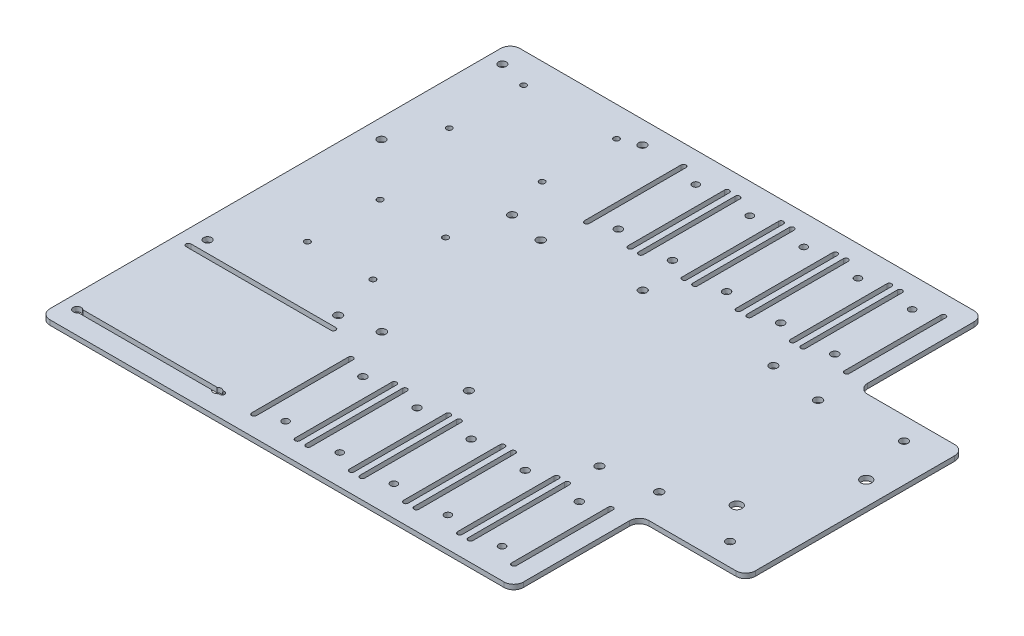
SolidWorks part; units mm, degrees
ref_plane "Front Plane" through (0, 0, 0) normal (0, 0, 1) x (1, 0, 0)
ref_plane "Top Plane" through (0, 0, 0) normal (0, 1, 0) x (1, 0, 0)
ref_plane "Right Plane" through (0, 0, 0) normal (1, 0, 0) x (0, 0, -1)
sketch "Sketch1" plane through (0, 0, 0) normal (0, 1, 0) x (1, 0, 0)
  line L1 (-261.1069, -365.6615) -> (261.1069, -365.6615)
  line L2 (-261.1069, -365.6615) -> (-261.1069, 365.6615)
  line L3 (-261.1069, 365.6615) -> (261.1069, 365.6615)
  line L4 (261.1069, -365.6615) -> (261.1069, 365.6615)
  line L5 (-261.1069, -365.6615) -> (261.1069, 365.6615) construction
  line L6 (-261.1069, 365.6615) -> (261.1069, -365.6615) construction
  point P0 (0, 0)
extrude "Boss-Extrude1" add sketch "Sketch1" along normal blind 3.175
sketch "Sketch3" plane through (0, 3.175, 0) normal (0, 1, 0) x (1, 0, 0)
  line L0 (-86.2012, -141.097) -> (-86.2012, -77.597) construction
  line L1 (91.1352, 52.197) -> (-91.1352, 52.197)
  line L2 (91.1352, 52.197) -> (91.1352, -52.197)
  line L3 (91.1352, -52.197) -> (-91.1352, -52.197)
  line L4 (-91.1352, 52.197) -> (-91.1352, -52.197)
  line L5 (91.1352, 52.197) -> (-91.1352, -52.197) construction
  line L6 (91.1352, -52.197) -> (-91.1352, 52.197) construction
  line L7 (-86.2012, -141.097) -> (-57.6262, -141.097)
  line L8 (-86.2012, -141.097) -> (-86.2012, -77.597)
  line L9 (-86.2012, -77.597) -> (-57.6262, -77.597)
  line L10 (-57.6262, -141.097) -> (-57.6262, -77.597)
  line L11 (-87.7887, -141.097) -> (-87.7887, -77.597)
  line L12 (-84.6138, -141.097) -> (-84.6138, -77.597)
  line L13 (-57.6262, -141.097) -> (-57.6262, -77.597) construction
  line L14 (-59.2137, -141.097) -> (-59.2137, -77.597)
  line L15 (-56.0388, -141.097) -> (-56.0388, -77.597)
  line L16 (-50.6412, -141.097) -> (-50.6412, -77.597) construction
  line L17 (-52.2287, -141.097) -> (-52.2287, -77.597)
  line L18 (-49.0538, -141.097) -> (-49.0538, -77.597)
  line L19 (-22.0662, -141.097) -> (-22.0662, -77.597) construction
  line L20 (-23.6537, -141.097) -> (-23.6537, -77.597)
  line L21 (-20.4788, -141.097) -> (-20.4788, -77.597)
  line L22 (-15.0812, -141.097) -> (-15.0812, -77.597) construction
  line L23 (-16.6687, -141.097) -> (-16.6687, -77.597)
  line L24 (-13.4938, -141.097) -> (-13.4938, -77.597)
  line L25 (13.4938, -141.097) -> (13.4938, -77.597) construction
  line L26 (11.9063, -141.097) -> (11.9063, -77.597)
  line L27 (15.0812, -141.097) -> (15.0812, -77.597)
  line L28 (20.4788, -141.097) -> (20.4788, -77.597) construction
  line L29 (18.8913, -141.097) -> (18.8913, -77.597)
  line L30 (22.0662, -141.097) -> (22.0662, -77.597)
  line L31 (49.0538, -141.097) -> (49.0538, -77.597) construction
  line L32 (47.4663, -141.097) -> (47.4663, -77.597)
  line L33 (50.6412, -141.097) -> (50.6412, -77.597)
  line L34 (56.0388, -141.097) -> (56.0388, -77.597) construction
  line L35 (54.4513, -141.097) -> (54.4513, -77.597)
  line L36 (57.6262, -141.097) -> (57.6262, -77.597)
  line L37 (84.6138, -141.097) -> (84.6138, -77.597) construction
  line L38 (83.0263, -141.097) -> (83.0263, -77.597)
  line L39 (86.2012, -141.097) -> (86.2012, -77.597)
  line L40 (-261.1069, 0) -> (261.1069, 0)
  line L41 (-261.1069, 365.6615) -> (-261.1069, -365.6615) construction
  line L42 (261.1069, -365.6615) -> (261.1069, 365.6615) construction
  line L43 (-86.2012, 141.097) -> (-86.2012, 77.597) construction
  line L44 (-87.7887, 141.097) -> (-87.7887, 77.597)
  line L45 (-84.6138, 141.097) -> (-84.6138, 77.597)
  line L46 (-57.6262, 141.097) -> (-57.6262, 77.597) construction
  line L47 (-59.2137, 141.097) -> (-59.2137, 77.597)
  line L48 (-56.0388, 141.097) -> (-56.0388, 77.597)
  line L49 (-50.6412, 141.097) -> (-50.6412, 77.597) construction
  line L50 (-52.2287, 141.097) -> (-52.2287, 77.597)
  line L51 (-49.0538, 141.097) -> (-49.0538, 77.597)
  line L52 (-22.0662, 141.097) -> (-22.0662, 77.597) construction
  line L53 (-23.6537, 141.097) -> (-23.6537, 77.597)
  line L54 (-20.4788, 141.097) -> (-20.4788, 77.597)
  line L55 (-15.0812, 141.097) -> (-15.0812, 77.597) construction
  line L56 (-16.6687, 141.097) -> (-16.6687, 77.597)
  line L57 (-13.4938, 141.097) -> (-13.4938, 77.597)
  line L58 (13.4938, 141.097) -> (13.4938, 77.597) construction
  line L59 (11.9063, 141.097) -> (11.9063, 77.597)
  line L60 (15.0812, 141.097) -> (15.0812, 77.597)
  line L61 (20.4788, 141.097) -> (20.4788, 77.597) construction
  line L62 (18.8913, 141.097) -> (18.8913, 77.597)
  line L63 (22.0662, 141.097) -> (22.0662, 77.597)
  line L64 (49.0538, 141.097) -> (49.0538, 77.597) construction
  line L65 (47.4663, 141.097) -> (47.4663, 77.597)
  line L66 (50.6412, 141.097) -> (50.6412, 77.597)
  line L67 (56.0388, 141.097) -> (56.0388, 77.597) construction
  line L68 (54.4513, 141.097) -> (54.4513, 77.597)
  line L69 (57.6262, 141.097) -> (57.6262, 77.597)
  line L70 (84.6138, 141.097) -> (84.6138, 77.597) construction
  line L71 (83.0263, 141.097) -> (83.0263, 77.597)
  line L72 (86.2012, 141.097) -> (86.2012, 77.597)
  arc A0 (-87.7887, -141.097) -> (-84.6138, -141.097) centre (-86.2012, -141.097) ccw
  arc A1 (-84.6138, -77.597) -> (-87.7887, -77.597) centre (-86.2012, -77.597) ccw
  arc A2 (-59.2137, -141.097) -> (-56.0388, -141.097) centre (-57.6262, -141.097) ccw
  arc A3 (-56.0388, -77.597) -> (-59.2137, -77.597) centre (-57.6262, -77.597) ccw
  arc A4 (-52.2287, -141.097) -> (-49.0538, -141.097) centre (-50.6412, -141.097) ccw
  arc A5 (-49.0538, -77.597) -> (-52.2287, -77.597) centre (-50.6412, -77.597) ccw
  arc A6 (-23.6537, -141.097) -> (-20.4788, -141.097) centre (-22.0662, -141.097) ccw
  arc A7 (-20.4788, -77.597) -> (-23.6537, -77.597) centre (-22.0662, -77.597) ccw
  arc A8 (-16.6687, -141.097) -> (-13.4938, -141.097) centre (-15.0812, -141.097) ccw
  arc A9 (-13.4938, -77.597) -> (-16.6687, -77.597) centre (-15.0812, -77.597) ccw
  arc A10 (11.9063, -141.097) -> (15.0812, -141.097) centre (13.4938, -141.097) ccw
  arc A11 (15.0812, -77.597) -> (11.9063, -77.597) centre (13.4938, -77.597) ccw
  arc A12 (18.8913, -141.097) -> (22.0662, -141.097) centre (20.4788, -141.097) ccw
  arc A13 (22.0662, -77.597) -> (18.8913, -77.597) centre (20.4788, -77.597) ccw
  arc A14 (47.4663, -141.097) -> (50.6412, -141.097) centre (49.0538, -141.097) ccw
  arc A15 (50.6412, -77.597) -> (47.4663, -77.597) centre (49.0538, -77.597) ccw
  arc A16 (54.4513, -141.097) -> (57.6262, -141.097) centre (56.0388, -141.097) ccw
  arc A17 (57.6262, -77.597) -> (54.4513, -77.597) centre (56.0388, -77.597) ccw
  arc A18 (83.0263, -141.097) -> (86.2012, -141.097) centre (84.6138, -141.097) ccw
  arc A19 (86.2012, -77.597) -> (83.0263, -77.597) centre (84.6138, -77.597) ccw
  arc A20 (-87.7887, 141.097) -> (-84.6138, 141.097) centre (-86.2012, 141.097) cw
  arc A21 (-84.6138, 77.597) -> (-87.7887, 77.597) centre (-86.2012, 77.597) cw
  arc A22 (-59.2137, 141.097) -> (-56.0388, 141.097) centre (-57.6262, 141.097) cw
  arc A23 (-56.0388, 77.597) -> (-59.2137, 77.597) centre (-57.6262, 77.597) cw
  arc A24 (-52.2287, 141.097) -> (-49.0538, 141.097) centre (-50.6412, 141.097) cw
  arc A25 (-49.0538, 77.597) -> (-52.2287, 77.597) centre (-50.6412, 77.597) cw
  arc A26 (-23.6537, 141.097) -> (-20.4788, 141.097) centre (-22.0662, 141.097) cw
  arc A27 (-20.4788, 77.597) -> (-23.6537, 77.597) centre (-22.0662, 77.597) cw
  arc A28 (-16.6687, 141.097) -> (-13.4938, 141.097) centre (-15.0812, 141.097) cw
  arc A29 (-13.4938, 77.597) -> (-16.6687, 77.597) centre (-15.0812, 77.597) cw
  arc A30 (11.9063, 141.097) -> (15.0812, 141.097) centre (13.4938, 141.097) cw
  arc A31 (15.0812, 77.597) -> (11.9063, 77.597) centre (13.4938, 77.597) cw
  arc A32 (18.8913, 141.097) -> (22.0662, 141.097) centre (20.4788, 141.097) cw
  arc A33 (22.0662, 77.597) -> (18.8913, 77.597) centre (20.4788, 77.597) cw
  arc A34 (47.4663, 141.097) -> (50.6412, 141.097) centre (49.0538, 141.097) cw
  arc A35 (50.6412, 77.597) -> (47.4663, 77.597) centre (49.0538, 77.597) cw
  arc A36 (54.4513, 141.097) -> (57.6262, 141.097) centre (56.0388, 141.097) cw
  arc A37 (57.6262, 77.597) -> (54.4513, 77.597) centre (56.0388, 77.597) cw
  arc A38 (83.0263, 141.097) -> (86.2012, 141.097) centre (84.6138, 141.097) cw
  arc A39 (86.2012, 77.597) -> (83.0263, 77.597) centre (84.6138, 77.597) cw
  circle A40 centre (-91.1352, -52.197) radius 2.667
  circle A41 centre (-91.1352, 52.197) radius 2.667
  circle A42 centre (91.1352, -52.197) radius 2.667
  circle A43 centre (91.1352, 52.197) radius 2.667
  point P0 (0, 0)
  point P10 (-86.2012, -109.347)
  point P15 (-57.6262, -109.347)
  point P26 (-50.6412, -109.347)
  point P31 (-22.0662, -109.347)
  point P40 (-15.0812, -109.347)
  point P45 (13.4938, -109.347)
  point P54 (20.4788, -109.347)
  point P59 (49.0538, -109.347)
  point P68 (56.0388, -109.347)
  point P73 (84.6138, -109.347)
  point P84 (-86.2012, 109.347)
  point P91 (-57.6262, 109.347)
  point P98 (-50.6412, 109.347)
  point P105 (-22.0662, 109.347)
  point P112 (-15.0812, 109.347)
  point P119 (13.4938, 109.347)
  point P126 (20.4788, 109.347)
  point P133 (49.0538, 109.347)
  point P140 (56.0388, 109.347)
  point P147 (84.6138, 109.347)
  dimension "D6" = 5.334
  dimension "D7" = 5.334
  dimension "D8" = 5.334
  dimension "D1" = 63.5
  dimension "D2" = 28.575
  dimension "D3" = 25.4
  dimension "D4" = 4.934
  dimension "D9" = 104.394
  dimension "D10" = 182.2704
  dimension "D5" = 5
extrude "Cut-Extrude2" cut sketch "Sketch3" against normal through all contours L9 A1 L11 A0 L7 L8 | L7 L12 L9 L8 | L14 L7 L10 L9 | L15 A3 L9 L10 L7 A2 | L18 A5 L17 A4 | L21 A7 L20 A6 | L24 A9 L23 A8 | L27 A11 L26 A10 | L30 A13 L29 A12 | L33 A15 L32 A14 | L36 A17 L35 A16 | L39 A19 L38 A18 | L3 A40 L4 | L4 A40 L3 | L1 A41 L4 | L4 A41 L1 | L2 A43 L1 | L1 A43 L2 | L3 A42 L2 | L2 A42 L3 | A39 L72 A38 L71 | A35 L66 A34 L65 | A37 L69 A36 L68 | A31 L60 A30 L59 | A33 L63 A32 L62 | A27 L54 A26 L53 | A29 L57 A28 L56 | A23 L48 A22 L47 | A25 L51 A24 L50 | A21 L45 A20 L44
sketch "Sketch5" plane through (0, 3.175, 0) normal (0, 1, 0) x (1, 0, 0)
  line L0 (-87.7887, -141.097) -> (-87.7887, -77.597) construction
  line L4 (-84.6138, -141.097) -> (-110.8495, -141.097)
  line L6 (0, 0) -> (-135.1006, 0)
  circle A0 centre (-71.8468, -134.747) radius 2.2479
  circle A1 centre (-71.8468, -83.947) radius 2.4434
  circle A2 centre (70.3932, 83.947) radius 2.4434
  arc A3 (-87.7887, -141.097) -> (-84.6138, -141.097) centre (-86.2012, -141.097) ccw construction
  circle A4 centre (-36.2868, -134.747) radius 2.2479
  circle A5 centre (-36.2868, -83.947) radius 2.4434
  circle A6 centre (-0.7268, -134.747) radius 2.2479
  circle A7 centre (-0.7268, -83.947) radius 2.4434
  circle A8 centre (34.8332, -134.747) radius 2.2479
  circle A9 centre (34.8332, -83.947) radius 2.4434
  circle A10 centre (70.3932, -134.747) radius 2.2479
  circle A11 centre (70.3932, -83.947) radius 2.4434
  circle A12 centre (70.3932, 134.747) radius 2.2479
  circle A13 centre (34.8332, 83.947) radius 2.4434
  circle A14 centre (34.8332, 134.747) radius 2.2479
  circle A15 centre (-0.7268, 83.947) radius 2.4434
  circle A16 centre (-0.7268, 134.747) radius 2.2479
  circle A17 centre (-36.2868, 83.947) radius 2.4434
  circle A18 centre (-36.2868, 134.747) radius 2.2479
  circle A19 centre (-71.8468, 83.947) radius 2.4434
  circle A20 centre (-71.8468, 134.747) radius 2.2479
  dimension "D1" = 50.8
  dimension "D2" = 15.942
  dimension "D3" = 6.35
  dimension "D4" = 5
extrude "Cut-Extrude3" cut sketch "Sketch5" against normal through all contours A1 | A0 | A4 | A5 | A11 | A10 | A9 | A8 | A6 | A7 | A2 | A13 | A14 | A12 | A16 | A15 | A17 | A18 | A20 | A19
sketch "Sketch8" plane through (0, 3.175, 0) normal (0, 1, 0) x (1, 0, 0)
  line L1 (152.2412, -34.3885) -> (124.3012, -34.3885)
  line L2 (152.2412, -34.3885) -> (152.2412, 22.7615)
  line L3 (152.2412, 22.7615) -> (124.3012, 22.7615)
  line L4 (124.3012, -34.3885) -> (124.3012, 22.7615)
  line L5 (86.2012, 141.097) -> (86.2012, 77.597) construction
  line L6 (261.1069, 365.6615) -> (-261.1069, 365.6615) construction
  circle A3 centre (124.3012, -34.3885) radius 3.556
  circle A4 centre (152.2412, 22.7615) radius 3.556
  dimension "D1" = 342.9
  dimension "D2" = 57.15
  dimension "D3" = 27.94
  dimension "D4" = 38.1
extrude "Cut-Extrude6" cut sketch "Sketch8" against normal through all contours L2 A4 L3 | L3 A4 L2 | L4 A3 L1 | L1 A3 L4
sketch "Sketch9" plane through (0, 3.175, 0) normal (0, 1, 0) x (1, 0, 0)
  line L0 (-87.7887, 141.097) -> (-87.7887, 77.597) construction
  line L1 (-166.9237, -25.3492) -> (-123.8707, -25.3492)
  line L2 (-166.9237, -25.3492) -> (-166.9237, 22.4028)
  line L3 (-166.9237, 22.4028) -> (-123.8707, 22.4028)
  line L4 (-123.8707, -25.3492) -> (-123.8707, 22.4028)
  line L5 (-184.9069, 85.9028) -> (-123.8707, 85.9028)
  line L6 (-184.9069, 85.9028) -> (-184.9069, 134.747)
  line L7 (-184.9069, 134.747) -> (-123.8707, 134.747)
  line L8 (-123.8707, 85.9028) -> (-123.8707, 134.747)
  line L10 (-57.6262, 141.097) -> (-86.2012, 141.097)
  circle A0 centre (-166.9237, -25.3492) radius 1.905
  circle A1 centre (-166.9237, 22.4028) radius 1.905
  circle A2 centre (-123.8707, -25.3492) radius 1.905
  circle A3 centre (-123.8707, 22.4028) radius 1.905
  circle A4 centre (-184.9069, 85.9028) radius 1.839
  circle A5 centre (-184.9069, 134.747) radius 1.839
  circle A6 centre (-123.8707, 134.747) radius 1.839
  circle A7 centre (-123.8707, 85.9028) radius 1.839
  dimension "D3" = 3.81
  dimension "D4" = 3.81
  dimension "D5" = 3.81
  dimension "D6" = 3.81
  dimension "D9" = 3.6779
  dimension "D10" = 3.6779
  dimension "D11" = 3.6779
  dimension "D12" = 3.6779
  dimension "D1" = 43.053
  dimension "D2" = 47.752
  dimension "D7" = 48.8442
  dimension "D8" = 61.0362
  dimension "D13" = 0
  dimension "D14" = 63.5
  dimension "D15" = 36.082
  dimension "D16" = 6.35
extrude "Cut-Extrude7" cut sketch "Sketch9" against normal through all contours L2 A0 L1 | L1 A0 L2 | L3 A1 L2 | L2 A1 L3 | L4 A3 L3 | L3 A3 L4 | L4 A2 L1 | L1 A2 L4 | L8 A7 L5 | L5 A7 L8 | L8 A6 L7 | L7 A6 L8 | L6 A5 L7 | L7 A5 L6 | L6 A4 L5 | L5 A4 L6
sketch "Sketch10" plane through (0, 3.175, 0) normal (0, 1, 0) x (1, 0, 0)
  line L0 (-261.1069, 0) -> (-20.9803, 0)
  line L1 (-203.9569, -139.5095) -> (-108.7069, -139.5095)
  line L2 (-203.9569, -139.5095) -> (-203.9569, -66.4845)
  line L3 (-203.9569, -66.4845) -> (-108.7069, -66.4845)
  line L4 (-108.7069, -139.5095) -> (-108.7069, -66.4845)
  line L5 (-261.1069, 365.6615) -> (-261.1069, -365.6615) construction
  line L6 (-203.9569, -139.5095) -> (-108.7069, -139.5095) construction
  line L7 (-203.9569, -137.922) -> (-108.7069, -137.922)
  line L8 (-203.9569, -141.097) -> (-108.7069, -141.097)
  line L9 (-203.9569, -66.4845) -> (-108.7069, -66.4845) construction
  line L10 (-203.9569, -64.897) -> (-108.7069, -64.897)
  line L11 (-203.9569, -68.072) -> (-108.7069, -68.072)
  line L12 (-86.2012, -141.097) -> (-57.6262, -141.097)
  line L13 (-87.7887, -141.097) -> (-87.7887, -77.597) construction
  arc A0 (-203.9569, -137.922) -> (-203.9569, -141.097) centre (-203.9569, -139.5095) ccw
  arc A1 (-108.7069, -141.097) -> (-108.7069, -137.922) centre (-108.7069, -139.5095) ccw
  arc A2 (-203.9569, -64.897) -> (-203.9569, -68.072) centre (-203.9569, -66.4845) ccw
  arc A3 (-108.7069, -68.072) -> (-108.7069, -64.897) centre (-108.7069, -66.4845) ccw
  point P9 (-156.3319, -139.5095)
  point P14 (-156.3319, -66.4845)
  dimension "D1" = 73.025
  dimension "D2" = 95.25
  dimension "D3" = 0
  dimension "D4" = 20.9182
  dimension "D5" = 3.175
  dimension "D6" = 3.175
extrude "Cut-Extrude9" cut sketch "Sketch10" against normal through all contours L8 A1 L4 L1 L2 A0 | L7 L2 L1 L4 | L2 L11 L4 L3 | L4 A3 L10 A2 L2 L3
sketch "Sketch11" plane through (0, 3.175, 0) normal (0, 1, 0) x (1, 0, 0)
  line L0 (-261.1069, 365.6615) -> (-261.1069, -365.6615) construction
  line L1 (-261.1069, -179.197) -> (261.1069, -179.197)
  line L2 (-261.1069, -179.197) -> (-261.1069, 179.197)
  line L3 (-261.1069, 179.197) -> (261.1069, 179.197)
  line L4 (261.1069, -179.197) -> (261.1069, 179.197)
  line L5 (261.1069, -365.6615) -> (261.1069, 365.6615) construction
  line L7 (-261.1069, -179.197) -> (261.1069, -179.197)
  line L8 (-261.1069, -179.197) -> (-261.1069, -365.6615)
  line L9 (-261.1069, -365.6615) -> (261.1069, -365.6615)
  line L10 (261.1069, -179.197) -> (261.1069, -365.6615)
  line L11 (-261.1069, 179.197) -> (261.1069, 179.197)
  line L12 (-261.1069, 179.197) -> (-261.1069, 365.6615)
  line L13 (-261.1069, 365.6615) -> (261.1069, 365.6615)
  line L14 (261.1069, 179.197) -> (261.1069, 365.6615)
  circle A0 centre (-71.8468, -134.747) radius 2.2479 construction
  circle A1 centre (-71.8468, 134.747) radius 2.2479 construction
  dimension "D1" = 44.45
  dimension "D2" = 44.45
extrude "Cut-Extrude10" cut sketch "Sketch11" against normal through all contours L10 L1 L8 L9 | L3 L14 L13 L12
sketch "Sketch12" plane through (0, 3.175, 0) normal (0, 1, 0) x (1, 0, 0)
  line L0 (-261.1069, 179.197) -> (-925.7769, 179.197)
  line L2 (-261.1069, -179.197) -> (-505.1609, -179.197)
  line L3 (-261.1069, -179.197) -> (-261.1069, 179.197)
  line L4 (-261.1069, 179.197) -> (-505.1609, 179.197)
  line L5 (-505.1609, -179.197) -> (-505.1609, 179.197)
extrude "Boss-Extrude3" add sketch "Sketch12" against normal blind 3.175 contours L5 L2 L3 L0
sketch "Sketch14" plane through (0, 0, 0) normal (0, -1, 0) x (1, 0, 0)
  line L0 (-505.1609, -179.197) -> (261.1069, -179.197) construction
  line L1 (-350.04, -179.197) -> (199.6192, -179.197)
  line L2 (-350.04, -179.197) -> (-350.04, 179.197)
  line L3 (-350.04, 179.197) -> (199.6192, 179.197)
  line L4 (199.6192, -179.197) -> (199.6192, 179.197)
  line L5 (-505.1609, 179.197) -> (261.1069, 179.197) construction
  line L6 (261.1069, 179.197) -> (261.1069, -179.197) construction
  line L7 (-350.04, -179.197) -> (-505.1609, -179.197)
  line L8 (-350.04, -179.197) -> (-350.04, 179.197)
  line L9 (-350.04, 179.197) -> (-505.1609, 179.197)
  line L10 (-505.1609, -179.197) -> (-505.1609, 179.197)
  line L11 (199.6192, -179.197) -> (261.1069, -179.197)
  line L12 (199.6192, -179.197) -> (199.6192, 179.197)
  line L13 (199.6192, 179.197) -> (261.1069, 179.197)
  line L14 (261.1069, -179.197) -> (261.1069, 179.197)
extrude "Cut-Extrude12" cut sketch "Sketch14" against normal through all contours L11 L14 L13 L4 | L10 L7 L2 L9
sketch "Sketch15" plane through (0, 0, 0) normal (0, -1, 0) x (1, 0, 0)
  line L0 (-350.04, -179.197) -> (199.6192, -179.197) construction
  line L1 (-213.376, -179.197) -> (167.624, -179.197)
  line L2 (-213.376, -179.197) -> (-213.376, 179.197)
  line L3 (-213.376, 179.197) -> (167.624, 179.197)
  line L4 (167.624, -179.197) -> (167.624, 179.197)
  line L5 (-350.04, 179.197) -> (199.6192, 179.197) construction
  line L6 (-350.04, 0) -> (199.6192, 0)
  line L7 (-350.04, -179.197) -> (-350.04, 179.197) construction
  line L8 (199.6192, -179.197) -> (199.6192, 179.197) construction
  line L10 (213.376, 154.4204) -> (-213.376, 154.4204)
  line L11 (213.376, 154.4204) -> (213.376, -154.4204)
  line L12 (213.376, -154.4204) -> (-213.376, -154.4204)
  line L13 (-213.376, 154.4204) -> (-213.376, -154.4204)
  line L14 (213.376, 154.4204) -> (-213.376, -154.4204) construction
  line L15 (213.376, -154.4204) -> (-213.376, 154.4204) construction
  line L16 (-350.04, -179.197) -> (-213.376, -179.197)
  line L17 (-350.04, -179.197) -> (-350.04, 179.197)
  line L18 (-350.04, 179.197) -> (-213.376, 179.197)
  line L19 (-213.376, -179.197) -> (-213.376, 179.197)
  line L20 (-213.376, 179.197) -> (199.6192, 179.197)
  line L21 (-213.376, 179.197) -> (-213.376, 154.4204)
  line L22 (-213.376, 154.4204) -> (199.6192, 154.4204)
  line L23 (199.6192, 179.197) -> (199.6192, 154.4204)
  line L24 (-213.376, -179.197) -> (199.6192, -179.197)
  line L25 (-213.376, -179.197) -> (-213.376, -154.4204)
  line L26 (-213.376, -154.4204) -> (199.6192, -154.4204)
  line L27 (199.6192, -179.197) -> (199.6192, -154.4204)
  line L28 (199.6192, -154.4204) -> (167.624, -154.4204)
  line L29 (199.6192, -154.4204) -> (199.6192, 154.4204)
  line L30 (199.6192, 154.4204) -> (167.624, 154.4204)
  line L31 (167.624, -154.4204) -> (167.624, 154.4204)
  point P14 (0, 0)
  dimension "D1" = 381
extrude "Cut-Extrude13" cut sketch "Sketch15" against normal through all contours L18 L17 L6 L2 | L17 L16 L2 L6 | L10 L4 L3 L2 | L4 L12 L2 L1 | L23 L20 L4 L10 | L6 L29 L10 L4 | L12 L29 L6 L4 | L24 L27 L12 L4
sketch "Sketch16" plane through (0, 0, 0) normal (0, -1, 0) x (1, 0, 0)
  line L0 (-213.376, 0) -> (167.624, 0)
  line L1 (-200.7354, -57.15) -> (142.1646, -57.15) construction
  line L2 (-200.7354, -57.15) -> (-200.7354, 57.15) construction
  line L3 (-200.7354, 57.15) -> (142.1646, 57.15) construction
  line L4 (142.1646, -57.15) -> (142.1646, 57.15) construction
  line L5 (-213.376, -154.4204) -> (-213.376, 154.4204) construction
  line L6 (167.624, -154.4204) -> (167.624, 154.4204) construction
  circle A0 centre (-200.7354, -57.15) radius 2.6
  circle A1 centre (-114.8834, -57.15) radius 2.6
  circle A2 centre (-29.0314, -57.15) radius 2.6
  circle A3 centre (56.8206, -57.15) radius 2.6
  circle A4 centre (142.6726, -57.15) radius 2.6
  circle A5 centre (-200.7354, 57.15) radius 2.6
  circle A6 centre (-114.8834, 57.15) radius 2.6
  circle A7 centre (-29.0314, 57.15) radius 2.6
  circle A8 centre (56.8206, 57.15) radius 2.6
  circle A9 centre (142.6726, 57.15) radius 2.6
  dimension "D4" = 5.2
  dimension "D6" = 5.2
  dimension "D1" = 342.9
  dimension "D2" = 114.3
  dimension "D3" = 57.15
  dimension "D5" = 5
  dimension "D7" = 5
extrude "Cut-Extrude14" cut sketch "Sketch16" against normal through all contours A4 | A9 | A8 | A3 | A2 | A7 | A6 | A0 | A5 | A1
sketch "Sketch17" plane through (0, 0, 0) normal (0, -1, 0) x (-1, 0, 0)
  line L1 (203.8469, -139.7) -> (111.7719, -139.7)
  line L2 (203.8469, -139.7) -> (203.8469, 139.7)
  line L3 (203.8469, 139.7) -> (111.7719, 139.7)
  line L4 (111.7719, -139.7) -> (111.7719, 139.7)
  line L5 (111.7719, 139.7) -> (203.8469, 139.7)
  line L6 (111.7719, 139.7) -> (111.7719, 154.4204)
  line L7 (111.7719, 154.4204) -> (203.8469, 154.4204)
  line L8 (203.8469, 139.7) -> (203.8469, 154.4204)
  line L10 (203.8469, 154.4204) -> (213.376, 154.4204)
  line L11 (203.8469, 154.4204) -> (203.8469, -148.0704)
  line L12 (203.8469, -148.0704) -> (213.376, -148.0704)
  line L13 (213.376, 154.4204) -> (213.376, -148.0704)
  circle A5 centre (111.7719, -139.7) radius 2.6
  circle A6 centre (111.7719, -139.7) radius 5.14
  circle A7 centre (203.8469, -139.7) radius 2.6
  circle A8 centre (111.7719, 139.7) radius 2.6
  circle A9 centre (203.8469, 139.7) radius 2.6
extrude "Cut-Extrude15" cut sketch "Sketch17" against normal through all contours L2 A9 L8 | L3 A9 L2 | L8 A9 L3 | L6 A8 L4 | L4 A8 L5 | L5 A8 L6 | L4 A5 L1 | L1 A5 L4 | L11 A7 L2 | L1 A7 L11 | L2 A7 L1
sketch "Sketch18" plane through (0, 0, 0) normal (0, -1, 0) x (1, 0, 0)
  line L0 (167.624, 0) -> (144.5656, 0)
  line L1 (167.624, -154.4204) -> (97.774, -154.4204)
  line L2 (167.624, -154.4204) -> (167.624, -71.8704)
  line L3 (167.624, -71.8704) -> (97.774, -71.8704)
  line L4 (97.774, -154.4204) -> (97.774, -71.8704)
  line L5 (167.624, -154.4204) -> (167.624, 154.4204) construction
  line L6 (97.774, 154.4204) -> (97.774, 71.8704)
  line L7 (167.624, 71.8704) -> (97.774, 71.8704)
  line L8 (167.624, 154.4204) -> (167.624, 71.8704)
  line L9 (167.624, 154.4204) -> (97.774, 154.4204)
  dimension "D1" = 82.55
  dimension "D2" = 69.85
extrude "Cut-Extrude16" cut sketch "Sketch18" against normal through all contours L4 L1 L2 L3 | L8 L9 L6 L7
fillet "Fillet2" radius 6.35 8 edges at (97.774, 1.5875, -71.8704) (167.624, 1.5875, 71.8704) (97.774, 1.5875, 71.8704) (97.774, 1.5875, 154.4204) (-213.376, 1.5875, 154.4204) (-213.376, 1.5875, -154.4204) (97.774, 1.5875, -154.4204) (167.624, 1.5875, -71.8704)
